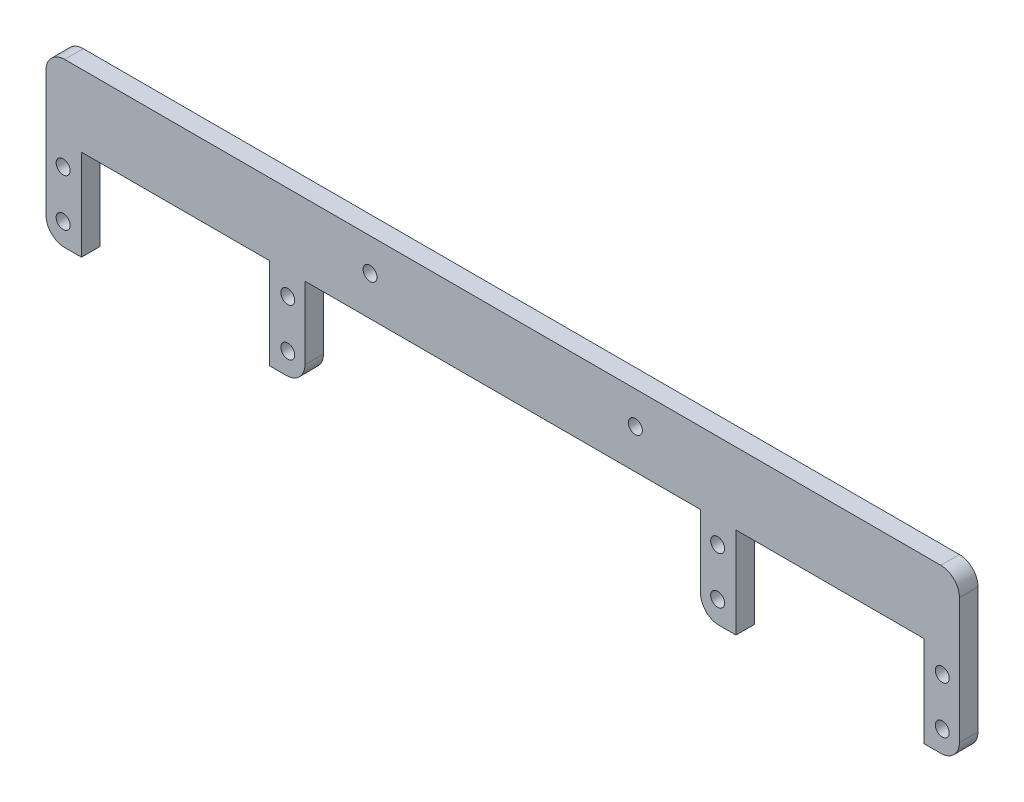
SolidWorks part; units mm, degrees
ref_plane "Front Plane" through (0, 0, 0) normal (0, 0, 1) x (1, 0, 0)
ref_plane "Top Plane" through (0, 0, 0) normal (0, 1, 0) x (1, 0, 0)
ref_plane "Right Plane" through (0, 0, 0) normal (1, 0, 0) x (0, 0, -1)
sketch "Sketch2" plane through (0, 0, 0) normal (0, 0, 1) x (1, 0, 0)
  line L0 (-67.0811, 16.9235) -> (-26.6951, 16.9235)
  line L1 (-26.6951, 16.9235) -> (-26.6951, -2.6345)
  line L2 (-26.6951, -2.6345) -> (-19.0751, -2.6345)
  line L3 (-19.0751, -2.6345) -> (-19.0751, 32.3655)
  line L4 (-19.0751, 32.3655) -> (-67.0811, 32.3655)
  line L5 (-207.7071, 16.9235) -> (-167.2319, 16.7363)
  line L6 (-74.7011, 16.9235) -> (-74.7011, -2.6345)
  line L7 (-74.7011, -2.6345) -> (-67.0811, -2.6345)
  line L8 (-67.0811, -2.6345) -> (-67.0811, 16.9235)
  line L9 (-67.0811, 16.9235) -> (-67.1703, 16.7363)
  line L10 (-74.7011, 32.3655) -> (-67.0811, 32.3655)
  line L11 (-159.7011, 16.9235) -> (-74.7011, 16.9235)
  line L12 (-167.3211, 32.3655) -> (-159.7011, 32.3655)
  line L13 (-167.3211, 16.9235) -> (-167.2319, 16.7363)
  line L14 (-167.3211, -2.6345) -> (-167.3211, 16.9235)
  line L15 (-159.7011, -2.6345) -> (-167.3211, -2.6345)
  line L16 (-159.7011, 16.9235) -> (-159.7011, -2.6345)
  line L18 (-215.3271, 32.3655) -> (-167.3211, 32.3655)
  line L19 (-215.3271, -2.6345) -> (-215.3271, 32.3655)
  line L20 (-207.7071, -2.6345) -> (-215.3271, -2.6345)
  line L21 (-207.7071, 16.9235) -> (-207.7071, -2.6345)
  line L22 (-167.3211, 16.9235) -> (-207.7071, 16.9235)
  line L23 (-159.7011, 32.3655) -> (-74.7011, 32.3655)
extrude "Boss-Extrude2" add sketch "Sketch2" along normal blind 4
fillet "Fillet1" radius 4 6 edges at (-74.7011, -2.6345, 2) (-159.7011, -2.6345, 2) (-215.3271, -2.6345, 2) (-19.0751, -2.6345, 2) (-215.3271, 32.3655, 2) (-19.0751, 32.3655, 2)
sketch "Sketch3" plane through (0, 0, 4) normal (0, 0, 1) x (1, 0, 0)
  line L0 (-211.3271, 32.3655) -> (-23.0751, 32.3655) construction
  line L2 (-159.7011, 16.9235) -> (-159.7011, 1.3655) construction
  line L4 (-74.7011, 16.9235) -> (-74.7011, 1.3655) construction
  circle A0 centre (-145.7011, 25.3655) radius 1.5
  circle A1 centre (-88.7011, 25.3655) radius 1.5
  dimension "D1" = 7
  dimension "D2" = 14
  dimension "D3" = 14
  dimension "D4" = 7
sketch "Sketch6" plane through (0, 0, 4) normal (0, 0, 1) x (1, 0, 0)
  line L0 (-67.0811, -2.6345) -> (-67.0811, 16.9235) construction
  line L1 (-167.3211, 16.9235) -> (-207.7071, 16.9235) construction
  line L2 (-207.7071, 16.9235) -> (-207.7071, -2.6345) construction
  line L3 (-67.0811, 16.9235) -> (-26.6951, 16.9235) construction
  circle A0 centre (-211.6441, 12.2245) radius 1.5
  circle A1 centre (-163.3841, 12.2245) radius 1.5
  circle A2 centre (-163.3841, 2.0645) radius 1.5
  circle A3 centre (-211.6441, 2.0645) radius 1.5
  circle A4 centre (-71.0181, 12.2245) radius 1.5
  circle A5 centre (-22.7581, 12.2245) radius 1.5
  circle A6 centre (-22.7581, 2.0645) radius 1.5
  circle A7 centre (-71.0181, 2.0645) radius 1.5
  dimension "D1" = 4.699
  dimension "D2" = 3.937
  dimension "D5" = 3.937
  dimension "D6" = 4.699
  dimension "D3" = 2
  dimension "D4" = 2
  dimension "D7" = 2
  dimension "D8" = 2
extrude "Cut-Extrude1" cut sketch "Sketch6" against normal blind 4
extrude "Cut-Extrude2" cut sketch "Sketch3" against normal blind 4 contours A0 | A1
